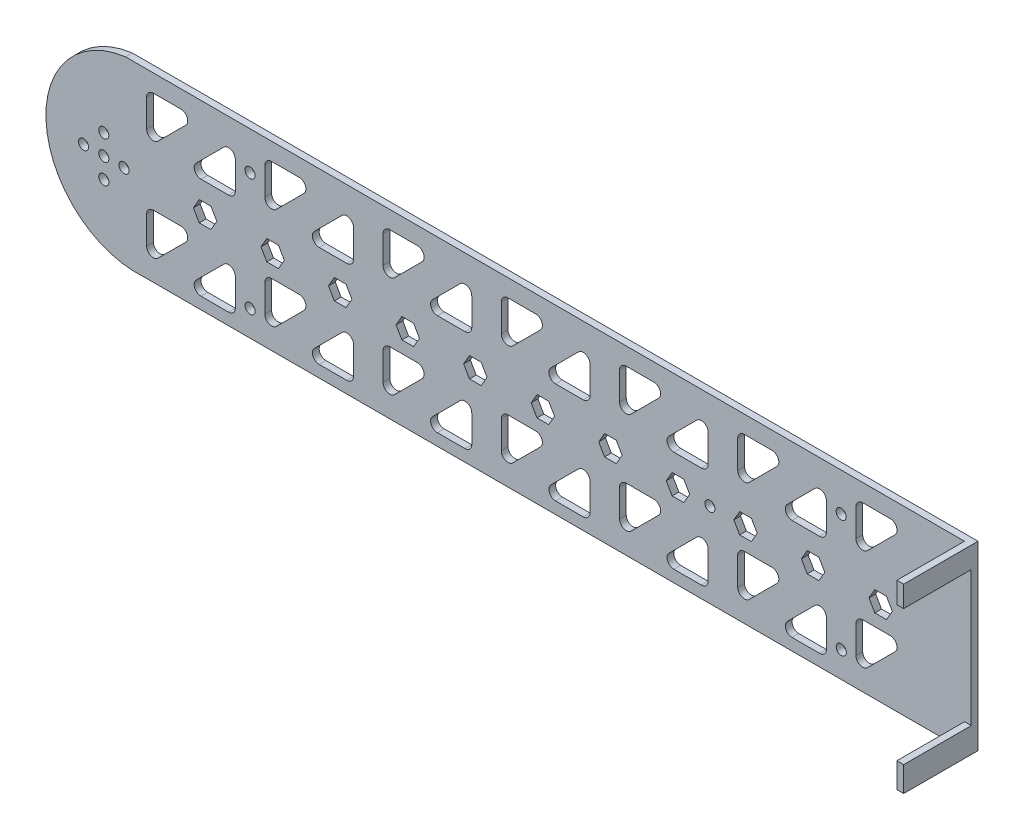
SolidWorks part; units mm, degrees
ref_plane "Ön Düzlem" through (0, 0, 0) normal (0, 0, 1) x (1, 0, 0)
ref_plane "Üst Düzlem" through (0, 0, 0) normal (0, 1, 0) x (1, 0, 0)
ref_plane "Sağ Düzlem" through (0, 0, 0) normal (1, 0, 0) x (0, 0, -1)
sketch "Çizim1" plane through (0, 0, 0) normal (0, 0, 1) x (1, 0, 0)
  line L0 (0, 34.9435) -> (0, -25.0192) construction
  line L1 (-123.6821, 28.6804) -> (123.6821, 28.6804)
  line L3 (-118.1627, -25.0192) -> (118.1627, -25.0192)
  line L5 (-150.2336, 30.0467) -> (150, -30) construction
  line L6 (123.6821, 28.6804) -> (137.2391, 28.6804)
  line L7 (-0.1168, 0.0234) -> (-130.1063, 0.0234) construction
  line L8 (-130.1063, 6.0234) -> (-130.1063, -6.1534) construction
  line L9 (-18.3887, -2.9789) -> (-16.6527, 0.0189)
  line L10 (1.6113, -2.9789) -> (3.3473, 0.0189)
  line L11 (3.3473, 0.0189) -> (1.6191, 3.0211)
  line L12 (1.6191, 3.0211) -> (-1.845, 3.0256)
  line L13 (-1.845, 3.0256) -> (-3.5809, 0.0279)
  line L14 (-3.5809, 0.0279) -> (-1.8528, -2.9744)
  line L15 (-1.8528, -2.9744) -> (1.6113, -2.9789)
  line L16 (-16.6527, 0.0189) -> (-18.3809, 3.0211)
  line L17 (-18.3809, 3.0211) -> (-21.845, 3.0256)
  line L18 (-21.845, 3.0256) -> (-23.5809, 0.0279)
  line L19 (-23.5809, 0.0279) -> (-21.8528, -2.9744)
  line L20 (-21.8528, -2.9744) -> (-18.3887, -2.9789)
  line L21 (-38.3887, -2.9789) -> (-36.6527, 0.0189)
  line L22 (-36.6527, 0.0189) -> (-38.3809, 3.0211)
  line L23 (-38.3809, 3.0211) -> (-41.845, 3.0256)
  line L24 (-41.845, 3.0256) -> (-43.5809, 0.0279)
  line L25 (-43.5809, 0.0279) -> (-41.8528, -2.9744)
  line L26 (-41.8528, -2.9744) -> (-38.3887, -2.9789)
  line L27 (-58.3887, -2.9789) -> (-56.6527, 0.0189)
  line L28 (-56.6527, 0.0189) -> (-58.3809, 3.0211)
  line L29 (-58.3809, 3.0211) -> (-61.845, 3.0256)
  line L30 (-61.845, 3.0256) -> (-63.5809, 0.0279)
  line L31 (-63.5809, 0.0279) -> (-61.8528, -2.9744)
  line L32 (-61.8528, -2.9744) -> (-58.3887, -2.9789)
  line L33 (-78.3887, -2.9789) -> (-76.6527, 0.0189)
  line L34 (-76.6527, 0.0189) -> (-78.3809, 3.0211)
  line L35 (-78.3809, 3.0211) -> (-81.845, 3.0256)
  line L36 (-81.845, 3.0256) -> (-83.5809, 0.0279)
  line L37 (-83.5809, 0.0279) -> (-81.8528, -2.9744)
  line L38 (-81.8528, -2.9744) -> (-78.3887, -2.9789)
  line L39 (-98.3887, -2.9789) -> (-96.6527, 0.0189)
  line L40 (-96.6527, 0.0189) -> (-98.3809, 3.0211)
  line L41 (-98.3809, 3.0211) -> (-101.845, 3.0256)
  line L42 (-101.845, 3.0256) -> (-103.5809, 0.0279)
  line L43 (-103.5809, 0.0279) -> (-101.8528, -2.9744)
  line L44 (-101.8528, -2.9744) -> (-98.3887, -2.9789)
  line L45 (21.6113, -2.9789) -> (23.3473, 0.0189)
  line L46 (18.1472, -2.9744) -> (21.6113, -2.9789)
  line L47 (16.4191, 0.0279) -> (18.1472, -2.9744)
  line L48 (18.155, 3.0256) -> (16.4191, 0.0279)
  line L49 (21.6191, 3.0211) -> (18.155, 3.0256)
  line L50 (23.3473, 0.0189) -> (21.6191, 3.0211)
  line L51 (41.6113, -2.9789) -> (43.3473, 0.0189)
  line L52 (38.1472, -2.9744) -> (41.6113, -2.9789)
  line L53 (36.4191, 0.0279) -> (38.1472, -2.9744)
  line L54 (38.155, 3.0256) -> (36.4191, 0.0279)
  line L55 (41.6191, 3.0211) -> (38.155, 3.0256)
  line L56 (43.3473, 0.0189) -> (41.6191, 3.0211)
  line L57 (61.6113, -2.9789) -> (63.3473, 0.0189)
  line L58 (58.1472, -2.9744) -> (61.6113, -2.9789)
  line L59 (56.4191, 0.0279) -> (58.1472, -2.9744)
  line L60 (58.155, 3.0256) -> (56.4191, 0.0279)
  line L61 (61.6191, 3.0211) -> (58.155, 3.0256)
  line L62 (63.3473, 0.0189) -> (61.6191, 3.0211)
  line L63 (81.6113, -2.9789) -> (83.3473, 0.0189)
  line L64 (78.1472, -2.9744) -> (81.6113, -2.9789)
  line L65 (76.4191, 0.0279) -> (78.1472, -2.9744)
  line L66 (78.155, 3.0256) -> (76.4191, 0.0279)
  line L67 (81.6191, 3.0211) -> (78.155, 3.0256)
  line L68 (83.3473, 0.0189) -> (81.6191, 3.0211)
  line L69 (101.6113, -2.9789) -> (103.3473, 0.0189)
  line L70 (98.1472, -2.9744) -> (101.6113, -2.9789)
  line L71 (96.4191, 0.0279) -> (98.1472, -2.9744)
  line L72 (98.155, 3.0256) -> (96.4191, 0.0279)
  line L73 (101.6191, 3.0211) -> (98.155, 3.0256)
  line L74 (103.3473, 0.0189) -> (101.6191, 3.0211)
  line L75 (-117.433, 15.462) -> (117.433, 15.462) construction
  line L76 (-117.433, 21.4866) -> (-117.433, 13.315)
  line L77 (-115.433, 23.4866) -> (-107.2614, 23.4866)
  line L78 (-105.8472, 20.0724) -> (-114.0187, 11.9008)
  line L79 (-94.5849, 20.0724) -> (-102.7565, 11.9008)
  line L80 (-101.3423, 8.4866) -> (-93.1707, 8.4866)
  line L81 (-91.1707, 10.4866) -> (-91.1707, 18.6582)
  line L82 (-82.433, 21.4866) -> (-82.433, 13.315)
  line L83 (-80.433, 23.4866) -> (-72.2614, 23.4866)
  line L84 (-70.8472, 20.0724) -> (-79.0187, 11.9008)
  line L85 (-59.5849, 20.0724) -> (-67.7565, 11.9008)
  line L86 (-66.3423, 8.4866) -> (-58.1707, 8.4866)
  line L87 (-56.1707, 10.4866) -> (-56.1707, 18.6582)
  line L88 (-47.433, 21.4866) -> (-47.433, 13.315)
  line L89 (-45.433, 23.4866) -> (-37.2614, 23.4866)
  line L90 (-35.8472, 20.0724) -> (-44.0187, 11.9008)
  line L91 (-24.5849, 20.0724) -> (-32.7565, 11.9008)
  line L92 (-31.3423, 8.4866) -> (-23.1707, 8.4866)
  line L93 (-21.1707, 10.4866) -> (-21.1707, 18.6582)
  line L94 (-12.433, 21.4866) -> (-12.433, 13.315)
  line L95 (-10.433, 23.4866) -> (-2.2614, 23.4866)
  line L96 (-0.8472, 20.0724) -> (-9.0187, 11.9008)
  line L97 (10.4151, 20.0724) -> (2.2435, 11.9008)
  line L98 (3.6577, 8.4866) -> (11.8293, 8.4866)
  line L99 (13.8293, 10.4866) -> (13.8293, 18.6582)
  line L100 (22.567, 21.4866) -> (22.567, 13.315)
  line L101 (24.567, 23.4866) -> (32.7386, 23.4866)
  line L102 (34.1528, 20.0724) -> (25.9813, 11.9008)
  line L103 (45.4151, 20.0724) -> (37.2435, 11.9008)
  line L104 (38.6577, 8.4866) -> (46.8293, 8.4866)
  line L105 (48.8293, 10.4866) -> (48.8293, 18.6582)
  line L106 (57.567, 21.4866) -> (57.567, 13.315)
  line L107 (59.567, 23.4866) -> (67.7386, 23.4866)
  line L108 (69.1528, 20.0724) -> (60.9813, 11.9008)
  line L109 (80.4151, 20.0724) -> (72.2435, 11.9008)
  line L110 (73.6577, 8.4866) -> (81.8293, 8.4866)
  line L111 (83.8293, 10.4866) -> (83.8293, 18.6582)
  line L112 (92.567, 21.4866) -> (92.567, 13.315)
  line L113 (94.567, 23.4866) -> (102.7386, 23.4866)
  line L114 (104.1528, 20.0724) -> (95.9813, 11.9008)
  line L118 (-82.433, -8.5134) -> (-82.433, -16.685)
  line L119 (-80.433, -6.5134) -> (-72.2614, -6.5134)
  line L120 (-70.8472, -9.9276) -> (-79.0187, -18.0992)
  line L121 (-59.5849, -9.9276) -> (-67.7565, -18.0992)
  line L122 (-66.3423, -21.5134) -> (-58.1707, -21.5134)
  line L123 (-56.1707, -19.5134) -> (-56.1707, -11.3418)
  line L124 (-47.433, -8.5134) -> (-47.433, -16.685)
  line L125 (-45.433, -6.5134) -> (-37.2614, -6.5134)
  line L126 (-35.8472, -9.9276) -> (-44.0187, -18.0992)
  line L127 (-24.5849, -9.9276) -> (-32.7565, -18.0992)
  line L128 (-31.3423, -21.5134) -> (-23.1707, -21.5134)
  line L129 (-21.1707, -19.5134) -> (-21.1707, -11.3418)
  line L130 (-12.433, -8.5134) -> (-12.433, -16.685)
  line L131 (-10.433, -6.5134) -> (-2.2614, -6.5134)
  line L132 (-0.8472, -9.9276) -> (-9.0187, -18.0992)
  line L133 (10.4151, -9.9276) -> (2.2435, -18.0992)
  line L134 (3.6577, -21.5134) -> (11.8293, -21.5134)
  line L135 (13.8293, -19.5134) -> (13.8293, -11.3418)
  line L136 (22.567, -8.5134) -> (22.567, -16.685)
  line L137 (24.567, -6.5134) -> (32.7386, -6.5134)
  line L138 (34.1528, -9.9276) -> (25.9813, -18.0992)
  line L139 (45.4151, -9.9276) -> (37.2435, -18.0992)
  line L140 (38.6577, -21.5134) -> (46.8293, -21.5134)
  line L141 (48.8293, -19.5134) -> (48.8293, -11.3418)
  line L142 (57.567, -8.5134) -> (57.567, -16.685)
  line L143 (59.567, -6.5134) -> (67.7386, -6.5134)
  line L144 (69.1528, -9.9276) -> (60.9813, -18.0992)
  line L145 (80.4151, -9.9276) -> (72.2435, -18.0992)
  line L146 (73.6577, -21.5134) -> (81.8293, -21.5134)
  line L147 (83.8293, -19.5134) -> (83.8293, -11.3418)
  line L148 (92.567, -8.5134) -> (92.567, -16.685)
  line L149 (94.567, -6.5134) -> (102.7386, -6.5134)
  line L150 (104.1528, -9.9276) -> (95.9813, -18.0992)
  line L154 (-117.433, -8.5134) -> (-117.433, -16.685)
  line L155 (-115.433, -6.5134) -> (-107.2614, -6.5134)
  line L156 (-105.8472, -9.9276) -> (-114.0187, -18.0992)
  line L157 (-94.5849, -9.9276) -> (-102.7565, -18.0992)
  line L158 (-101.3423, -21.5134) -> (-93.1707, -21.5134)
  line L159 (-91.1707, -19.5134) -> (-91.1707, -11.3418)
  line L160 (-0.1168, 0.0234) -> (126.9645, 1.6425) construction
  line L168 (108.6577, 8.4866) -> (116.8293, 8.4866) [skipped]
  line L169 (118.8293, 10.4866) -> (118.8293, 18.6582) [skipped]
  line L170 (118.8293, -19.5134) -> (118.8293, -11.3418) [skipped]
  line L171 (115.4151, -9.9276) -> (107.2435, -18.0992) [skipped]
  line L172 (108.6577, -21.5134) -> (116.8293, -21.5134) [skipped]
  line L173 (115.4151, 20.0724) -> (110.8046, 15.462) [skipped]
  line L176 (110.2391, 21.9008) -> (130.2391, -18.0992) construction
  line L177 (110.2391, -18.0992) -> (130.2391, 21.9008) construction
  line L178 (137.2391, -25.0192) -> (118.1627, -25.0192)
  line L179 (146.7064, 21.9008) -> (126.7064, 21.9008)
  line L180 (146.7468, -18.1182) -> (127.2163, -18.1182)
  line L181 (126.7064, 21.9008) -> (127.2226, -18.6158)
  line L182 (137.2391, 28.6804) -> (144.7064, 28.6804)
  line L183 (146.7064, 26.6804) -> (146.7064, 21.9008)
  line L184 (146.7468, -18.1182) -> (146.7468, -23.0192)
  line L185 (144.7468, -25.0192) -> (137.2391, -25.0192)
  arc A0 (-123.6821, 28.6804) -> (-118.1627, -25.0192) centre (-120.2391, 1.9008) ccw
  arc A1 (124.105, -24.821) -> (118.1627, -25.0192) centre (120.2391, 1.9008) cw
  circle A2 centre (-130.1063, 0.0234) radius 10
  circle A3 centre (-130.1063, 6.0234) radius 1.5
  circle A4 centre (-130.1063, -5.9766) radius 1.5
  circle A5 centre (-136.1063, 0.0234) radius 1.5
  circle A6 centre (-130.1063, 6.0234) radius 1.5
  circle A7 centre (-124.1063, 0.0234) radius 1.5
  circle A8 centre (-130.1063, 0.0234) radius 1.5
  circle A15 centre (-0.1168, 0.0234) radius 3 construction
  arc A16 (-101.3423, 8.4866) -> (-102.7565, 11.9008) centre (-101.3423, 10.4866) cw
  arc A17 (-93.1707, 8.4866) -> (-91.1707, 10.4866) centre (-93.1707, 10.4866) ccw
  arc A18 (-91.1707, 18.6582) -> (-94.5849, 20.0724) centre (-93.1707, 18.6582) ccw
  arc A19 (-114.0187, 11.9008) -> (-117.433, 13.315) centre (-115.433, 13.315) cw
  arc A20 (-107.2614, 23.4866) -> (-105.8472, 20.0724) centre (-107.2614, 21.4866) cw
  arc A21 (-117.433, 21.4866) -> (-115.433, 23.4866) centre (-115.433, 21.4866) cw
  arc A22 (-72.2614, 23.4866) -> (-70.8472, 20.0724) centre (-72.2614, 21.4866) cw
  arc A23 (-82.433, 21.4866) -> (-80.433, 23.4866) centre (-80.433, 21.4866) cw
  arc A24 (-79.0187, 11.9008) -> (-82.433, 13.315) centre (-80.433, 13.315) cw
  arc A25 (-66.3423, 8.4866) -> (-67.7565, 11.9008) centre (-66.3423, 10.4866) cw
  arc A26 (-58.1707, 8.4866) -> (-56.1707, 10.4866) centre (-58.1707, 10.4866) ccw
  arc A27 (-56.1707, 18.6582) -> (-59.5849, 20.0724) centre (-58.1707, 18.6582) ccw
  arc A28 (-37.2614, 23.4866) -> (-35.8472, 20.0724) centre (-37.2614, 21.4866) cw
  arc A29 (-47.433, 21.4866) -> (-45.433, 23.4866) centre (-45.433, 21.4866) cw
  arc A30 (-44.0187, 11.9008) -> (-47.433, 13.315) centre (-45.433, 13.315) cw
  arc A31 (-31.3423, 8.4866) -> (-32.7565, 11.9008) centre (-31.3423, 10.4866) cw
  arc A32 (-23.1707, 8.4866) -> (-21.1707, 10.4866) centre (-23.1707, 10.4866) ccw
  arc A33 (-21.1707, 18.6582) -> (-24.5849, 20.0724) centre (-23.1707, 18.6582) ccw
  arc A34 (-2.2614, 23.4866) -> (-0.8472, 20.0724) centre (-2.2614, 21.4866) cw
  arc A35 (-12.433, 21.4866) -> (-10.433, 23.4866) centre (-10.433, 21.4866) cw
  arc A36 (-9.0187, 11.9008) -> (-12.433, 13.315) centre (-10.433, 13.315) cw
  arc A37 (3.6577, 8.4866) -> (2.2435, 11.9008) centre (3.6577, 10.4866) cw
  arc A38 (11.8293, 8.4866) -> (13.8293, 10.4866) centre (11.8293, 10.4866) ccw
  arc A39 (13.8293, 18.6582) -> (10.4151, 20.0724) centre (11.8293, 18.6582) ccw
  arc A40 (32.7386, 23.4866) -> (34.1528, 20.0724) centre (32.7386, 21.4866) cw
  arc A41 (22.567, 21.4866) -> (24.567, 23.4866) centre (24.567, 21.4866) cw
  arc A42 (25.9813, 11.9008) -> (22.567, 13.315) centre (24.567, 13.315) cw
  arc A43 (38.6577, 8.4866) -> (37.2435, 11.9008) centre (38.6577, 10.4866) cw
  arc A44 (46.8293, 8.4866) -> (48.8293, 10.4866) centre (46.8293, 10.4866) ccw
  arc A45 (48.8293, 18.6582) -> (45.4151, 20.0724) centre (46.8293, 18.6582) ccw
  arc A46 (67.7386, 23.4866) -> (69.1528, 20.0724) centre (67.7386, 21.4866) cw
  arc A47 (57.567, 21.4866) -> (59.567, 23.4866) centre (59.567, 21.4866) cw
  arc A48 (60.9813, 11.9008) -> (57.567, 13.315) centre (59.567, 13.315) cw
  arc A49 (73.6577, 8.4866) -> (72.2435, 11.9008) centre (73.6577, 10.4866) cw
  arc A50 (81.8293, 8.4866) -> (83.8293, 10.4866) centre (81.8293, 10.4866) ccw
  arc A51 (83.8293, 18.6582) -> (80.4151, 20.0724) centre (81.8293, 18.6582) ccw
  arc A52 (102.7386, 23.4866) -> (104.1528, 20.0724) centre (102.7386, 21.4866) cw
  arc A53 (92.567, 21.4866) -> (94.567, 23.4866) centre (94.567, 21.4866) cw
  arc A54 (95.9813, 11.9008) -> (92.567, 13.315) centre (94.567, 13.315) cw
  arc A58 (-72.2614, -6.5134) -> (-70.8472, -9.9276) centre (-72.2614, -8.5134) cw
  arc A59 (-82.433, -8.5134) -> (-80.433, -6.5134) centre (-80.433, -8.5134) cw
  arc A60 (-79.0187, -18.0992) -> (-82.433, -16.685) centre (-80.433, -16.685) cw
  arc A61 (-66.3423, -21.5134) -> (-67.7565, -18.0992) centre (-66.3423, -19.5134) cw
  arc A62 (-58.1707, -21.5134) -> (-56.1707, -19.5134) centre (-58.1707, -19.5134) ccw
  arc A63 (-56.1707, -11.3418) -> (-59.5849, -9.9276) centre (-58.1707, -11.3418) ccw
  arc A64 (-37.2614, -6.5134) -> (-35.8472, -9.9276) centre (-37.2614, -8.5134) cw
  arc A65 (-47.433, -8.5134) -> (-45.433, -6.5134) centre (-45.433, -8.5134) cw
  arc A66 (-44.0187, -18.0992) -> (-47.433, -16.685) centre (-45.433, -16.685) cw
  arc A67 (-31.3423, -21.5134) -> (-32.7565, -18.0992) centre (-31.3423, -19.5134) cw
  arc A68 (-23.1707, -21.5134) -> (-21.1707, -19.5134) centre (-23.1707, -19.5134) ccw
  arc A69 (-21.1707, -11.3418) -> (-24.5849, -9.9276) centre (-23.1707, -11.3418) ccw
  arc A70 (-2.2614, -6.5134) -> (-0.8472, -9.9276) centre (-2.2614, -8.5134) cw
  arc A71 (-12.433, -8.5134) -> (-10.433, -6.5134) centre (-10.433, -8.5134) cw
  arc A72 (-9.0187, -18.0992) -> (-12.433, -16.685) centre (-10.433, -16.685) cw
  arc A73 (3.6577, -21.5134) -> (2.2435, -18.0992) centre (3.6577, -19.5134) cw
  arc A74 (11.8293, -21.5134) -> (13.8293, -19.5134) centre (11.8293, -19.5134) ccw
  arc A75 (13.8293, -11.3418) -> (10.4151, -9.9276) centre (11.8293, -11.3418) ccw
  arc A76 (32.7386, -6.5134) -> (34.1528, -9.9276) centre (32.7386, -8.5134) cw
  arc A77 (22.567, -8.5134) -> (24.567, -6.5134) centre (24.567, -8.5134) cw
  arc A78 (25.9813, -18.0992) -> (22.567, -16.685) centre (24.567, -16.685) cw
  arc A79 (38.6577, -21.5134) -> (37.2435, -18.0992) centre (38.6577, -19.5134) cw
  arc A80 (46.8293, -21.5134) -> (48.8293, -19.5134) centre (46.8293, -19.5134) ccw
  arc A81 (48.8293, -11.3418) -> (45.4151, -9.9276) centre (46.8293, -11.3418) ccw
  arc A82 (67.7386, -6.5134) -> (69.1528, -9.9276) centre (67.7386, -8.5134) cw
  arc A83 (57.567, -8.5134) -> (59.567, -6.5134) centre (59.567, -8.5134) cw
  arc A84 (60.9813, -18.0992) -> (57.567, -16.685) centre (59.567, -16.685) cw
  arc A85 (73.6577, -21.5134) -> (72.2435, -18.0992) centre (73.6577, -19.5134) cw
  arc A86 (81.8293, -21.5134) -> (83.8293, -19.5134) centre (81.8293, -19.5134) ccw
  arc A87 (83.8293, -11.3418) -> (80.4151, -9.9276) centre (81.8293, -11.3418) ccw
  arc A88 (102.7386, -6.5134) -> (104.1528, -9.9276) centre (102.7386, -8.5134) cw
  arc A89 (92.567, -8.5134) -> (94.567, -6.5134) centre (94.567, -8.5134) cw
  arc A90 (95.9813, -18.0992) -> (92.567, -16.685) centre (94.567, -16.685) cw
  arc A94 (-107.2614, -6.5134) -> (-105.8472, -9.9276) centre (-107.2614, -8.5134) cw
  arc A95 (-117.433, -8.5134) -> (-115.433, -6.5134) centre (-115.433, -8.5134) cw
  arc A96 (-114.0187, -18.0992) -> (-117.433, -16.685) centre (-115.433, -16.685) cw
  arc A97 (-101.3423, -21.5134) -> (-102.7565, -18.0992) centre (-101.3423, -19.5134) cw
  arc A98 (-93.1707, -21.5134) -> (-91.1707, -19.5134) centre (-93.1707, -19.5134) ccw
  arc A99 (-91.1707, -11.3418) -> (-94.5849, -9.9276) centre (-93.1707, -11.3418) ccw
  arc A100 (116.8293, 8.4866) -> (118.8293, 10.4866) centre (116.8293, 10.4866) ccw [skipped]
  arc A101 (108.6577, 8.4866) -> (107.2435, 11.9008) centre (108.6577, 10.4866) cw [skipped]
  arc A102 (118.8293, -11.3418) -> (115.4151, -9.9276) centre (116.8293, -11.3418) ccw [skipped]
  arc A103 (108.6577, -21.5134) -> (107.2435, -18.0992) centre (108.6577, -19.5134) cw [skipped]
  arc A104 (118.8293, 18.6582) -> (115.4151, 20.0724) centre (116.8293, 18.6582) ccw [skipped]
  arc A105 (116.8293, -21.5134) -> (118.8293, -19.5134) centre (116.8293, -19.5134) ccw [skipped]
  arc A108 (144.7468, -25.0192) -> (146.7468, -23.0192) centre (144.7468, -23.0192) ccw
  arc A109 (144.7064, 28.6804) -> (146.7064, 26.6804) centre (144.7064, 26.6804) cw
  circle A110 centre (131.8598, 25.9008) radius 1.5
  circle A111 centre (141.8598, 25.9008) radius 1.5
  circle A112 centre (131.8598, -22.0992) radius 1.5
  circle A113 centre (141.8598, -22.0992) radius 1.5
  point P0 (0, 0)
  point P23 (120.3522, -2.2451)
  point P31 (-130.1063, 0.0234)
  point P124 (-117.433, 8.4866)
  point P127 (-102.433, 23.4866)
  point P130 (-117.433, 23.4866)
  dimension "D1" = 20
  dimension "D3" = 3
  dimension "D6" = 6
  dimension "D10" = 2
  dimension "D16" = 2
  dimension "D4" = 6
  dimension "D8" = 15
  dimension "D9" = 15
  dimension "D13" = 40
  dimension "D14" = 20
  dimension "D15" = 20
  dimension "D7" = 6
  dimension "D11" = 7
  dimension "D12" = 2
  dimension "D5" = 4
extrude "Yükseklik-Ekstrüzyon2" add sketch "Çizim1" along normal blind 2
sketch "Çizim9" plane through (0, 0, 0) normal (0, 0, -1) x (-1, 0, 0)
  line L0 (-92.567, 17.4008) -> (-83.8293, 17.4008) construction
  line L1 (-92.567, 21.4866) -> (-92.567, 13.315) construction
  line L2 (-83.8293, 10.4866) -> (-83.8293, 18.6582) construction
  line L3 (-88.1982, 17.4008) -> (-88.1982, -25.6798) construction
  line L4 (-96.4191, 0.0279) -> (-83.3473, 0.0189) construction
  line L5 (-1.8099, 9.7212) -> (-1.8099, -20.2788) construction
  line L6 (-96.4191, 0.0279) -> (96.6527, 0.0189) construction
  circle A0 centre (-88.1982, 17.4008) radius 1.5
  circle A1 centre (-88.2222, -17.3564) radius 1.5
  arc A2 (-3.6577, 8.4866) -> (-2.2435, 11.9008) centre (-3.6577, 10.4866) ccw construction
  arc A3 (-3.6577, -21.5134) -> (-2.2435, -18.0992) centre (-3.6577, -19.5134) ccw construction
  circle A4 centre (86.8018, 17.4008) radius 1.5
  circle A5 centre (86.7778, -17.3564) radius 1.5
  dimension "D1" = 2
extrude "Kes-Ekstrüzyon5" cut sketch "Çizim9" against normal blind 10
sketch "Çizim10" plane through (0, 0, 2) normal (0, 0, 1) x (1, 0, 0)
  circle A0 centre (49.3473, 0) radius 1.5
  dimension "D1" = 3
  dimension "D2" = 6
extrude "Kes-Ekstrüzyon7" cut sketch "Çizim10" against normal blind 10
sketch "Çizim11" plane through (0, 0, 2) normal (0, 0, 1) x (1, 0, 0)
  line L0 (-123.6821, 28.6804) -> (144.7064, 28.6804) construction
  line L1 (126.7064, 28.6804) -> (149.6239, 28.6804)
  line L2 (126.7064, 28.6804) -> (126.7064, -25.0192)
  line L3 (126.7064, -25.0192) -> (149.6239, -25.0192)
  line L4 (149.6239, 28.6804) -> (149.6239, -25.0192)
extrude "Kes-Ekstrüzyon8" cut sketch "Çizim11" against normal blind 10
sketch "Çizim12" plane through (0, 0, 2) normal (0, 0, 1) x (1, 0, 0)
  line L0 (-123.6821, 28.6804) -> (126.7064, 28.6804) construction
  line L1 (124.7064, 28.6804) -> (126.7064, 28.6804)
  line L2 (124.7064, 28.6804) -> (124.7064, -25.0192)
  line L3 (124.7064, -25.0192) -> (126.7064, -25.0192)
  line L4 (126.7064, 28.6804) -> (126.7064, -25.0192)
  dimension "D1" = 2
extrude "Yükseklik-Ekstrüzyon3" add sketch "Çizim12" along normal blind 20
sketch "Çizim13" plane through (126.7064, 0, 0) normal (1, 0, 0) x (0, 0, -1)
  line L0 (-2, 0.0184) -> (0, 0.0189) construction
  line L1 (-22, -25.0192) -> (-22, 28.6804) construction
  line L2 (0, 28.6804) -> (0, -25.0192) construction
  line L4 (-22, 2.408) -> (-22, -17.592)
  line L5 (-22, -17.592) -> (-2, -17.592)
  line L6 (-2, 2.408) -> (-2, -17.592)
  line L8 (-22, 2.408) -> (-22, 22.408)
  line L9 (-22, 22.408) -> (-2, 22.408)
  line L10 (-2, 2.408) -> (-2, 22.408)
  line L11 (0, -25.0192) -> (-22, -25.0192) construction
  dimension "D1" = 20
  dimension "D2" = 20
  dimension "D3" = 2
  dimension "8" = 7.4272
extrude "Kes-Ekstrüzyon10" cut sketch "Çizim13" against normal blind 20
